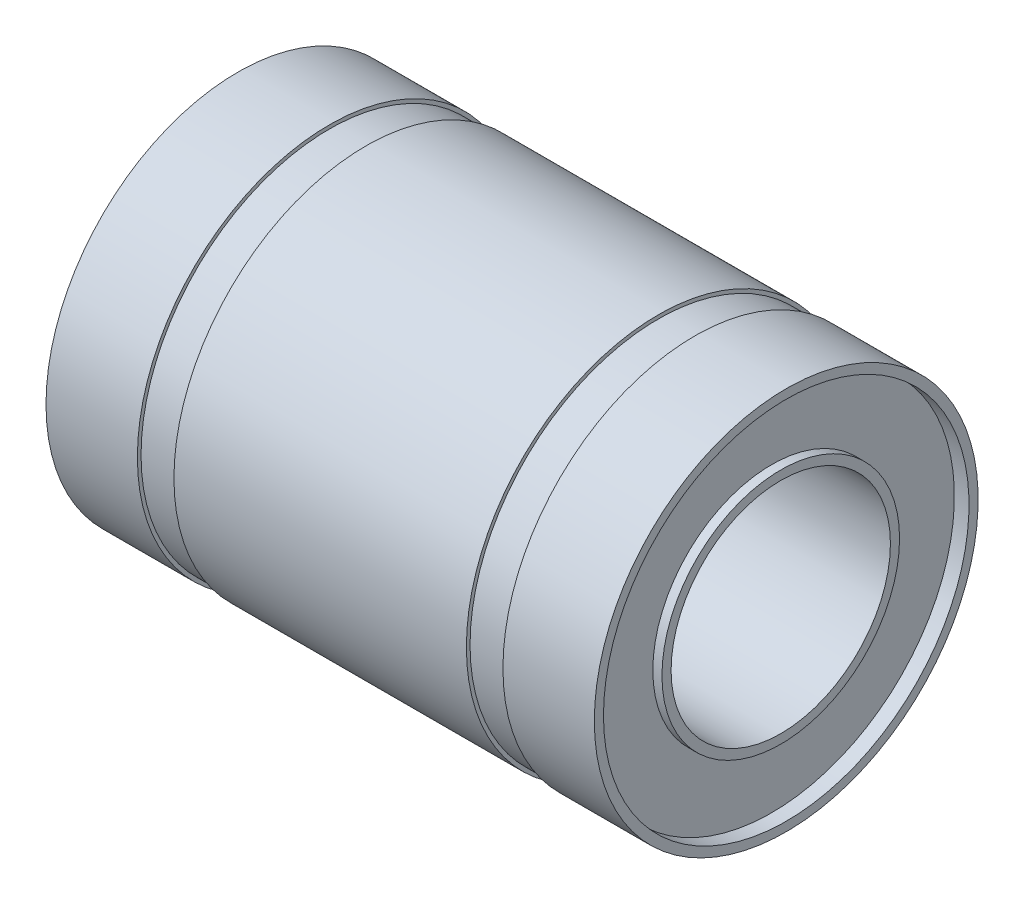
SolidWorks part; units mm, degrees
ref_plane "Front Plane" through (0, 0, 0) normal (0, 0, 1) x (1, 0, 0)
ref_plane "Top Plane" through (0, 0, 0) normal (0, 1, 0) x (1, 0, 0)
ref_plane "Right Plane" through (0, 0, 0) normal (1, 0, 0) x (0, 0, -1)
sketch "Sketch1" plane through (0, 0, 0) normal (0, 0, 1) x (1, 0, 0)
  line L0 (0, 72.5983) -> (0, 0) construction
  line L1 (0, 0) -> (122.6916, 0) construction
  line L2 (-8, 10.5) -> (8, 10.5)
  line L3 (8, 10.5) -> (8, 10.3)
  line L4 (8, 10.3) -> (10, 10.3)
  line L5 (10, 10.3) -> (10, 10.5)
  line L6 (10, 10.5) -> (15, 10.5)
  line L7 (15, 10.5) -> (15, 10)
  line L8 (15, 10) -> (14.2, 10)
  line L9 (14.2, 10) -> (14.2, 6.5)
  line L10 (14.2, 6.5) -> (14.7, 6.5)
  line L11 (14.7, 6.5) -> (14.7, 6)
  line L12 (14.7, 6) -> (-14.7, 6)
  line L13 (-14.7, 6.5) -> (-14.7, 6)
  line L14 (-14.2, 6.5) -> (-14.7, 6.5)
  line L15 (-14.2, 10) -> (-14.2, 6.5)
  line L16 (-15, 10) -> (-14.2, 10)
  line L17 (-15, 10.5) -> (-15, 10)
  line L18 (-10, 10.5) -> (-15, 10.5)
  line L19 (-10, 10.3) -> (-10, 10.5)
  line L20 (-8, 10.3) -> (-10, 10.3)
  line L21 (-8, 10.5) -> (-8, 10.3)
  line L22 (14.7, -6) -> (-14.7, -6) construction
  line L23 (10, -10.5) -> (15, -10.5) construction
  point P17 (0, 6)
  point P26 (0, 10.5)
  point P30 (0, 0)
  dimension "D1" = 0.2
  dimension "D2" = 12
  dimension "D3" = 21
  dimension "D4" = 0.5
  dimension "D5" = 0.5
  dimension "D6" = 0.5
  dimension "D7" = 0.8
  dimension "D8" = 30
  dimension "D9" = 2
  dimension "D10" = 5
revolve "Revolve1" add sketch "Sketch1" angle 360 about L1
